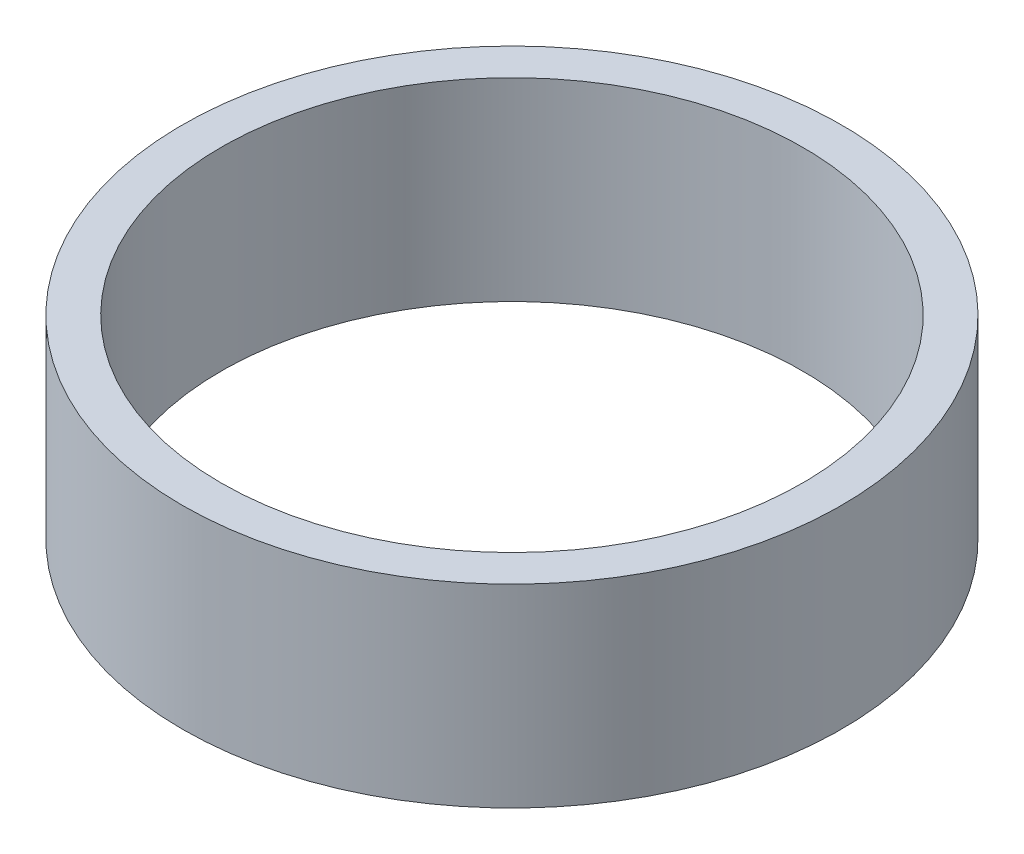
SolidWorks part; units mm, degrees
ref_plane "Front Plane" through (0, 0, 0) normal (0, 0, 1) x (1, 0, 0)
ref_plane "Top Plane" through (0, 0, 0) normal (0, 1, 0) x (1, 0, 0)
ref_plane "Right Plane" through (0, 0, 0) normal (1, 0, 0) x (0, 0, -1)
sketch "Sketch1" plane through (0, 0, 0) normal (0, 1, 0) x (1, 0, 0)
  circle A0 centre (0, 0) radius 30
  circle A1 centre (0, 0) radius 34
  dimension "D1" = 60
  dimension "D2" = 68
extrude "Boss-Extrude1" add sketch "Sketch1" along normal blind 20
